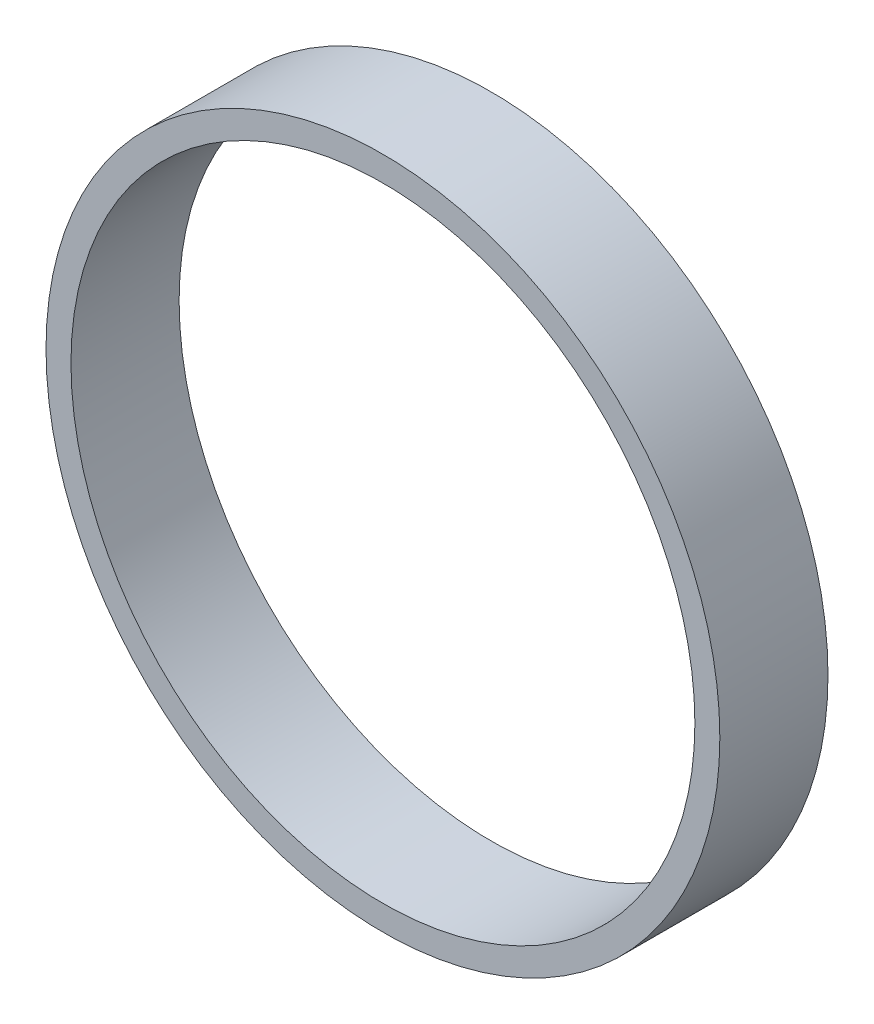
SolidWorks part; units mm, degrees
ref_plane "Front" through (0, 0, 0) normal (0, 0, 1) x (1, 0, 0)
ref_plane "Top" through (0, 0, 0) normal (0, 1, 0) x (1, 0, 0)
ref_plane "Right" through (0, 0, 0) normal (1, 0, 0) x (0, 0, -1)
sketch "Sketch4" plane through (0, 0, 0) normal (0, 0, 1) x (1, 0, 0)
  circle A0 centre (0, 0) radius 10.287
  dimension "D1" = 20.574
extrude "Boss-Extrude3" add sketch "Sketch4" along normal blind 3.302
sketch "Sketch5" plane through (0, 0, 3.302) normal (0, 0, 1) x (1, 0, 0)
  circle A0 centre (0, 0) radius 9.525
extrude "Cut-Extrude2" cut sketch "Sketch5" against normal through all
